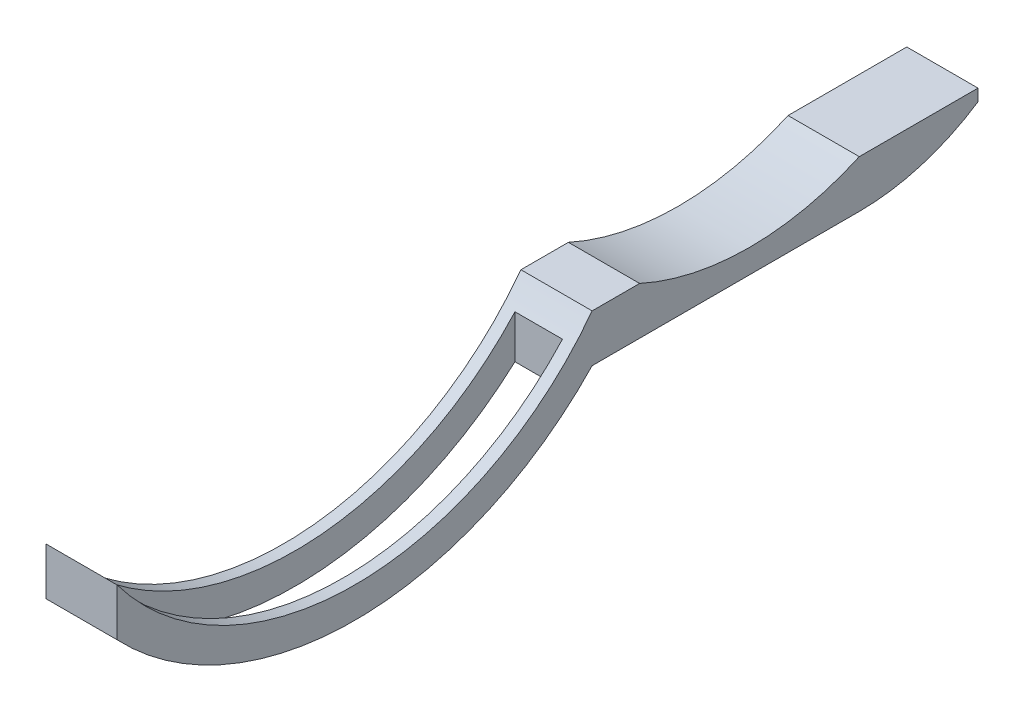
SolidWorks part; units mm, degrees
ref_plane "Front Plane" through (0, 0, 0) normal (0, 0, 1) x (1, 0, 0)
ref_plane "Top Plane" through (0, 0, 0) normal (0, 1, 0) x (1, 0, 0)
ref_plane "Right Plane" through (0, 0, 0) normal (1, 0, 0) x (0, 0, -1)
sketch "Sketch1" plane through (0, 0, 0) normal (1, 0, 0) x (0, 0, -1)
  line L0 (0, 0) -> (0, 8)
  line L1 (80, 0) -> (125, 0)
  line L2 (80, 0) -> (80, 8) construction
  line L3 (80, 8) -> (88, 8)
  line L4 (125, 8) -> (145, 8)
  line L5 (145, 8) -> (145, 6)
  line L6 (0, 8) -> (80, 8) construction
  line L7 (40, -12) -> (40, 8) construction
  line L8 (106.5, 4) -> (106.5, 0) construction
  line L9 (125, 8) -> (125, 0) construction
  arc A0 (0, 0) -> (80, 0) centre (40, 38) ccw
  arc A1 (0, 8) -> (80, 8) centre (40, 38) ccw
  arc A2 (88, 8) -> (125, 8) centre (106.5, 48.7812) ccw
  arc A3 (145, 6) -> (125, 0) centre (125, 36.3333) cw
  point P15 (160, 8)
  point P18 (179.7613, 8)
  dimension "D1" = 8
  dimension "D2" = 20
  dimension "D3" = 80
  dimension "D4" = 8
  dimension "D5" = 2
  dimension "D6" = 45
  dimension "D7" = 4
  dimension "D8" = 20
extrude "Boss-Extrude1" add sketch "Sketch1" along normal blind 12
sketch "Sketch2" plane through (0, 0, 0) normal (0, 1, 0) x (1, 0, 0)
  line L0 (12, 0) -> (0, 0) construction
  line L1 (2, 77) -> (10, 77)
  line L2 (2, 77) -> (2, 2)
  line L3 (2, 2) -> (10, 2)
  line L4 (10, 77) -> (10, 2)
  line L5 (0, 80) -> (0, 0) construction
  line L6 (12, 0) -> (12, 80) construction
  line L7 (12, 80) -> (0, 80) construction
  point P4 (9.1392, 4.4781)
  point P7 (6, 0)
  dimension "D1" = 2
  dimension "D2" = 2
  dimension "D3" = 2
  dimension "D4" = 3
extrude "Cut-Extrude1" cut sketch "Sketch2" against normal through all both and the other way through all
